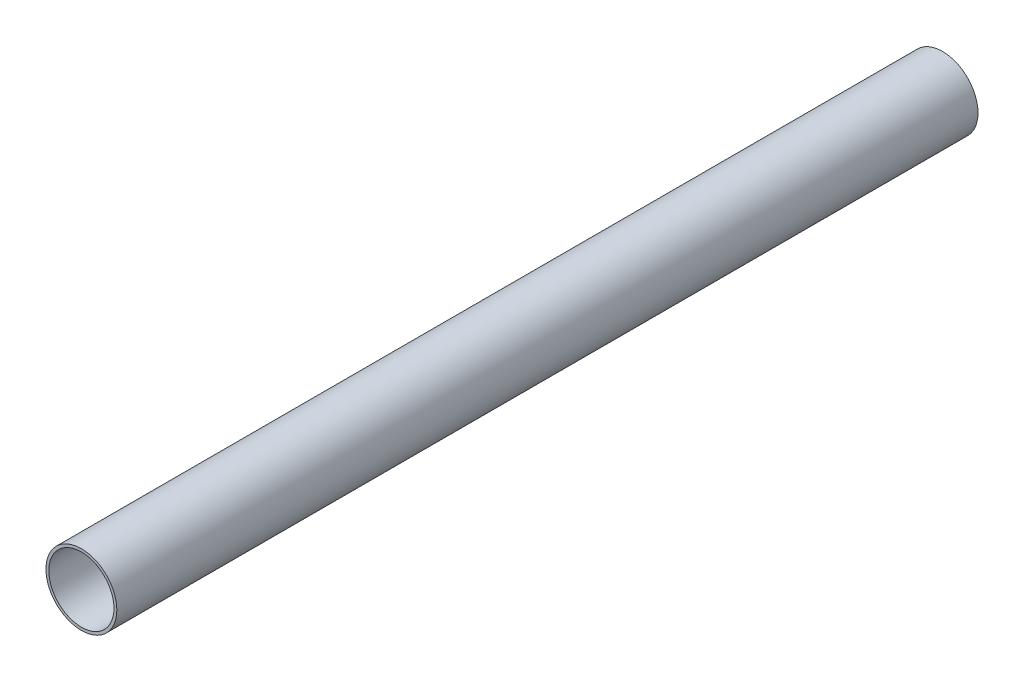
SolidWorks part; units mm, degrees
ref_plane "Front Plane" through (0, 0, 0) normal (0, 0, 1) x (1, 0, 0)
ref_plane "Top Plane" through (0, 0, 0) normal (0, 1, 0) x (1, 0, 0)
ref_plane "Right Plane" through (0, 0, 0) normal (1, 0, 0) x (0, 0, -1)
sketch "Sketch1" plane through (0, 0, 0) normal (0, 0, 1) x (1, 0, 0)
  circle A0 centre (0, 0) radius 12.35
  circle A1 centre (0, 0) radius 11.35
  dimension "D1" = 24.7
  dimension "D2" = 1
extrude "Boss-Extrude1" add sketch "Sketch1" along normal blind 300
